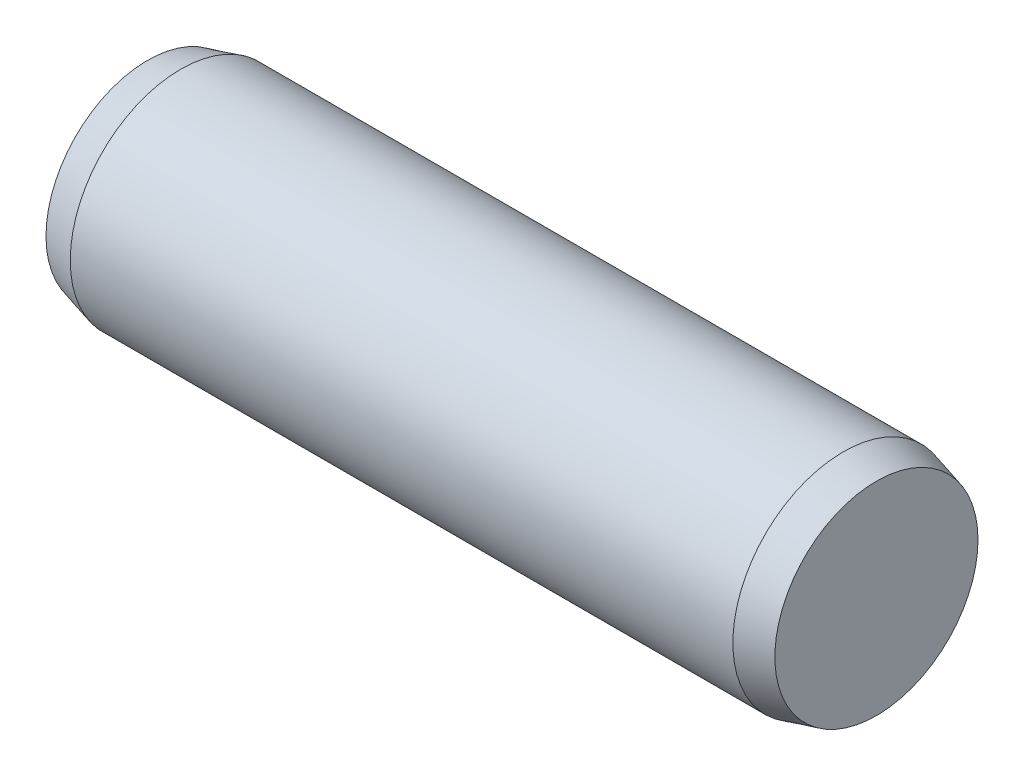
SolidWorks part; units mm, degrees
ref_plane "Front Plane" through (0, 0, 0) normal (0, 0, 1) x (1, 0, 0)
ref_plane "Top Plane" through (0, 0, 0) normal (0, 1, 0) x (1, 0, 0)
ref_plane "Right Plane" through (0, 0, 0) normal (1, 0, 0) x (0, 0, -1)
sketch "Sketch1" plane through (0, 0, 0) normal (0, 0, 1) x (1, 0, 0)
  line L0 (-6, 0) -> (6, 0) construction
  line L1 (6, 2) -> (6, -2) construction
  line L2 (-6, 2) -> (-6, -2) construction
  line L3 (6.6, 2) -> (6.6, -2) construction
  line L4 (-6.6, 2) -> (-6.6, -2) construction
  line L5 (-6, 0) -> (-6.6, 0) construction
  line L6 (6, 0) -> (6.6, 0) construction
  dimension "D1" = 0.6
  dimension "Dia" = 4
  dimension "Length" = 12
  dimension "C" = 0.6
sketch "Sketch2" plane through (0, 0, 0) normal (1, 0, 0) x (0, 0, -1)
  circle A0 centre (0, 0) radius 2
extrude "Extrude1" add sketch "Sketch2" against normal up to vertex (6 mm away) and the other way up to vertex (6 mm away) up to point (-6, 2, 0) other way up to point (6, 2, 0)
sketch "Sketch3" plane through (6, 0, 0) normal (1, 0, 0) x (0, 0, -1)
  circle A1 centre (0, 0) radius 2
  circle A2 centre (0, 0) radius 2
  dimension "D1" = 0
extrude "Extrude2" add sketch "Sketch3" along normal up to vertex (0.6 mm away) draft 15 up to point (6.6, 0, 0)
sketch "Sketch4" plane through (-6, 0, 0) normal (-1, 0, 0) x (0, 0, 1)
  circle A1 centre (0, 0) radius 2
  circle A2 centre (0, 0) radius 2
  dimension "D1" = 0
extrude "Extrude3" add sketch "Sketch4" along normal up to vertex (0.6 mm away) draft 15 up to point (-6.6, 0, 0)
equation "\"D1@Sketch1\" = \"C@Sketch1\""
